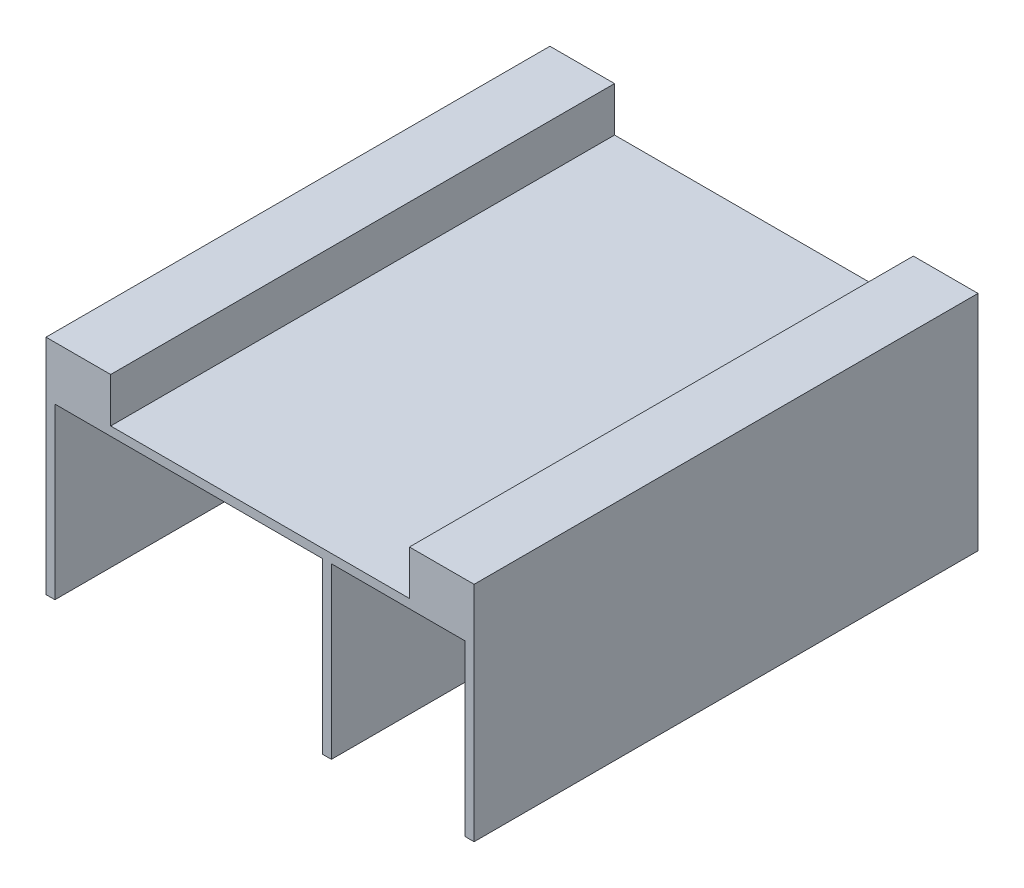
SolidWorks part; units mm, degrees
ref_plane "Front Plane" through (0, 0, 0) normal (0, 0, 1) x (1, 0, 0)
ref_plane "Top Plane" through (0, 0, 0) normal (0, 1, 0) x (1, 0, 0)
ref_plane "Right Plane" through (0, 0, 0) normal (1, 0, 0) x (0, 0, -1)
sketch "Эскиз1" plane through (0, 0, 0) normal (0, 1, 0) x (1, 0, 0)
  line L1 (0, 0) -> (96, 0)
  line L2 (0, 0) -> (0, 113)
  line L3 (0, 113) -> (96, 113)
  line L4 (96, 0) -> (96, 113)
  dimension "D1" = 113
  dimension "D2" = 96
extrude "Бобышка-Вытянуть1" add sketch "Эскиз1" along normal blind 50 contours L2 L3 L4 L1
sketch "Эскиз2" plane through (0, 50, 0) normal (0, 1, 0) x (1, 0, 0)
  line L0 (0, 113) -> (96, 113) construction
  line L1 (14.5, 113) -> (81.5, 113)
  line L2 (14.5, 113) -> (14.5, 0)
  line L3 (14.5, 0) -> (81.5, 0)
  line L4 (81.5, 113) -> (81.5, 0)
  line L5 (0, 0) -> (96, 0) construction
  line L6 (14.5, 100.3514) -> (0, 100.3514) construction
  line L7 (0, 0) -> (0, 113) construction
  line L8 (81.5, 100.3514) -> (96, 100.3514) construction
  line L9 (96, 0) -> (96, 113) construction
  dimension "D1" = 67
extrude "Вырез-Вытянуть1" cut sketch "Эскиз2" against normal blind 10
sketch "Эскиз3" plane through (0, 0, 0) normal (0, -1, 0) x (1, 0, 0)
  line L0 (0, 0) -> (96, 0) construction
  line L1 (2, 0) -> (62, 0)
  line L2 (2, 0) -> (2, -113)
  line L3 (2, -113) -> (62, -113)
  line L4 (62, 0) -> (62, -113)
  line L5 (0, -113) -> (96, -113) construction
  line L6 (0, 0) -> (0, -113) construction
  line L7 (64, 0) -> (94, 0)
  line L8 (64, 0) -> (64, -113)
  line L9 (64, -113) -> (94, -113)
  line L10 (94, 0) -> (94, -113)
  line L11 (96, 0) -> (96, -113) construction
  dimension "D1" = 2
  dimension "D2" = 2
  dimension "D3" = 2
  dimension "D4" = 60
extrude "Вырез-Вытянуть2" cut sketch "Эскиз3" against normal blind 38
sketch "Эскиз4" plane through (0, 0, 0) normal (-1, 0, 0) x (0, 0, 1)
  line L1 (-106, 36) -> (-26, 36)
  line L2 (-106, 36) -> (-106, 21)
  line L3 (-106, 21) -> (-26, 21)
  line L4 (-26, 36) -> (-26, 21)
  line L5 (0, 50) -> (-113, 50) construction
  line L8 (-113, 50) -> (-113, 0) construction
  point P4 (-104.7334, 38)
  point P8 (-111.0189, 38)
  dimension "D1" = 14
  dimension "D2" = 80
  dimension "D3" = 15
  dimension "D4" = 7
extrude "Вырез-Вытянуть3" cut sketch "Эскиз4" against normal blind 2
